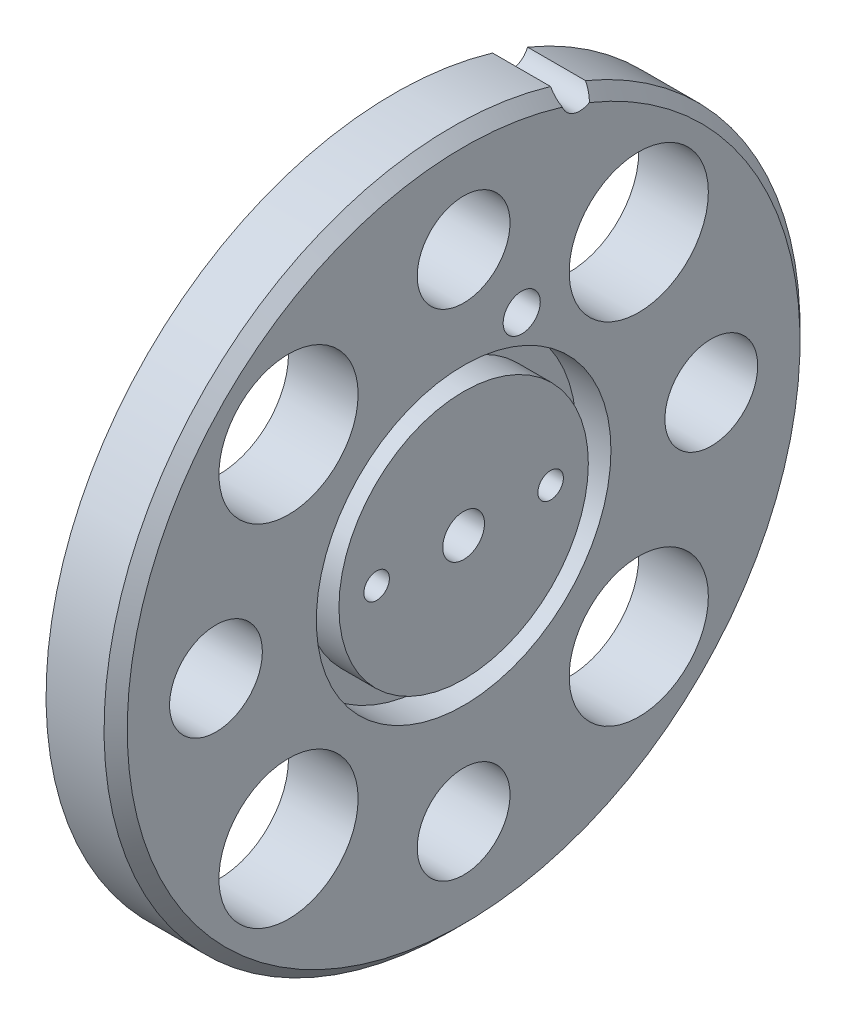
SolidWorks part; units mm, degrees
ref_plane "Plan de face" through (0, 0, 0) normal (0, 0, 1) x (1, 0, 0)
ref_plane "Plan de dessus" through (0, 0, 0) normal (0, 1, 0) x (1, 0, 0)
ref_plane "Plan de droite" through (0, 0, 0) normal (1, 0, 0) x (0, 0, -1)
sketch "Esquisse1" plane through (0, 0, 0) normal (1, 0, 0) x (0, 0, -1)
  line L0 (0, -13.2074) -> (0, 59.5533) construction
  line L1 (58.8329, 0) -> (-10.806, 0) construction
  line L2 (7.5, 9.1821) -> (7.5, -3.3292) construction
  line L3 (0, 0) -> (37.4492, 37.4492) construction
  line L4 (0, 0) -> (14.1398, 39.9297) construction
  arc A0 (8.4923, 28.7729) -> (11.5077, 27.7051) centre (0, 0) ccw
  circle A1 centre (0, 0) radius 1.8
  circle A2 centre (7.5, 0) radius 1.1
  circle A3 centre (-7.5, 0) radius 1.1
  circle A4 centre (15.0967, -15.0967) radius 6
  circle A5 centre (21.35, 0) radius 4
  arc A6 (8.4923, 28.7729) -> (11.5077, 27.7051) centre (10.0142, 28.2792) ccw
  circle A7 centre (0, 0) radius 10.75 construction
  circle A8 centre (0, 0) radius 12.7 construction
  circle A9 centre (0, 0) radius 21.35 construction
  circle A10 centre (15.0967, 15.0967) radius 6
  circle A11 centre (0, 21.35) radius 4
  circle A12 centre (-15.0967, -15.0967) radius 6
  circle A13 centre (0, -21.35) radius 4
  circle A14 centre (-15.0967, 15.0967) radius 6
  circle A15 centre (-21.35, 0) radius 4
  dimension "D1" = 7.5
  dimension "D2" = 45
  dimension "D3" = 4
  dimension "D4" = 19.5
extrude "Boss.-Extru.1" add sketch "Esquisse1" along normal blind 6
sketch "Esquisse2" plane through (6, 0, 0) normal (1, 0, 0) x (0, 0, -1)
  line L0 (0, -18.8341) -> (0, 33.8865) construction
  line L1 (0, 0) -> (12.3373, 34.8396) construction
  circle A0 centre (0, 0) radius 12.7
  circle A1 centre (0, 0) radius 15 construction
  circle A2 centre (5.0071, 14.1396) radius 1.6
  circle A3 centre (0, 0) radius 10.75
  dimension "D1" = 19.5
extrude "Enlèv. mat.-Extru.1" cut sketch "Esquisse2" against normal blind 3
chamfer "Chanfrein1" distance 1 angle 45 1 edges at (6, -28.2792, 10.0142)
